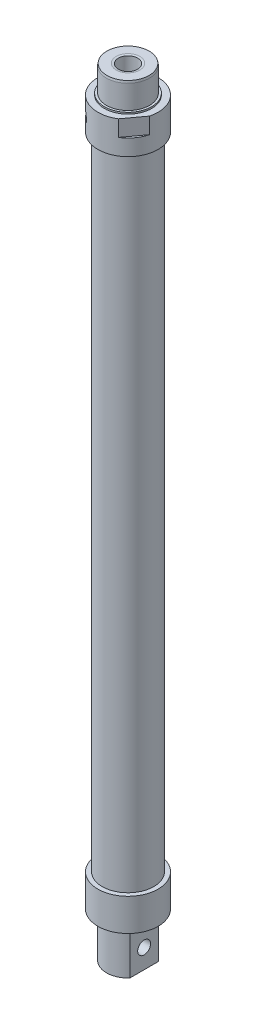
SolidWorks part; units mm, degrees
ref_plane "Front Plane" through (0, 0, 0) normal (0, 0, 1) x (1, 0, 0)
ref_plane "Top Plane" through (0, 0, 0) normal (0, 1, 0) x (1, 0, 0)
ref_plane "Right Plane" through (0, 0, 0) normal (1, 0, 0) x (0, 0, -1)
sketch "Sketch1" plane through (0, 0, 0) normal (0, 1, 0) x (1, 0, 0)
  circle A0 centre (0, 0) radius 12
  circle A1 centre (0, 0) radius 10
  dimension "D1" = 2
  dimension "D2" = 20
extrude "Boss-Extrude1" add sketch "Sketch1" along normal blind 298
sketch "Sketch2" plane through (0, 298, 0) normal (0, 1, 0) x (1, 0, 0)
  circle A0 centre (0, 0) radius 10
  circle A1 centre (0, 0) radius 14
  dimension "D1" = 20
  dimension "D2" = 4
extrude "Boss-Extrude2" add sketch "Sketch2" along normal blind 15
sketch "Sketch3" plane through (0, 313, 0) normal (0, 1, 0) x (1, 0, 0)
  line L0 (0, 0) -> (11.2894, -8.2795) construction
  line L1 (0, 0) -> (-9.5475, -10.2394) construction
  circle A0 centre (0, 0) radius 14 construction
ref_plane "Plane1" through (11.2894, 313, 8.2795) normal (0.8064, 0, 0.5914) x (0.5914, 0, -0.8064)
sketch "Sketch4" plane through (11.2894, 313, 8.2795) normal (0.8064, 0, 0.5914) x (0.5914, 0, -0.8064)
  line L0 (-6, 0) -> (6, 0)
  line L1 (-6, 0) -> (-6, -7.5)
  line L2 (6, 0) -> (6, -7.5)
  line L3 (-6, -7.5) -> (6, -7.5)
  dimension "D1" = 7.5
  dimension "D2" = 12
extrude "Cut-Extrude1" cut sketch "Sketch4" against normal blind 1 contours L0 L2 L3 L1
ref_plane "Plane2" through (0, 313, 0) normal (0.8064, 0, 0.5914) x (0.5914, 0, -0.8064)
mirror "Mirror1" about plane through (0, 313, 0) normal (0.8064, 0, 0.5914) of "Cut-Extrude1"
ref_plane "Plane3" through (-9.5475, 313, 10.2394) normal (-0.682, 0, 0.7314) x (0.7314, 0, 0.682)
sketch "Sketch5" plane through (-9.5475, 313, 10.2394) normal (-0.682, 0, 0.7314) x (0.7314, 0, 0.682)
  line L0 (0, 0) -> (13.9032, 0) construction
  circle A0 centre (0, -8) radius 2.5
  dimension "D2" = 5
  dimension "D1" = 8
extrude "Cut-Extrude2" cut sketch "Sketch5" against normal blind 5
sketch "Sketch6" plane through (0, 313, 0) normal (0, 1, 0) x (1, 0, 0)
  circle A0 centre (0, 0) radius 11
  dimension "D1" = 22
extrude "Boss-Extrude3" add sketch "Sketch6" along normal blind 0.75
sketch "Sketch7" plane through (0, 313.75, 0) normal (0, 1, 0) x (1, 0, 0)
  circle A0 centre (0, 0) radius 10
extrude "Boss-Extrude4" add sketch "Sketch7" along normal blind 12
sketch "Sketch9" plane through (0, 0, 0) normal (0, -1, 0) x (1, 0, 0)
  circle A0 centre (0, 0) radius 10
  circle A1 centre (0, 0) radius 14
  dimension "D1" = 20
  dimension "D2" = 4
extrude "Boss-Extrude6" add sketch "Sketch9" along normal blind 15
sketch "Sketch10" plane through (0, -15, 0) normal (0, -1, 0) x (1, 0, 0)
  circle A0 centre (0, 0) radius 11
  dimension "D1" = 22
extrude "Boss-Extrude7" add sketch "Sketch10" along normal blind 0.75
sketch "Sketch11" plane through (0, -15.75, 0) normal (0, -1, 0) x (1, 0, 0)
  circle A0 centre (0, 0) radius 10
  dimension "D1" = 20
extrude "Boss-Extrude8" add sketch "Sketch11" along normal blind 20
sketch "Sketch12" plane through (0, -35.75, 0) normal (0, -1, 0) x (1, 0, 0)
  line L0 (0, 0) -> (10, 0) construction
  line L1 (7.5, 6.6144) -> (7.5, -6.6144)
  line L2 (0, 10) -> (0, -10) construction
  line L3 (-7.5, 6.6144) -> (-7.5, -6.6144)
  circle A0 centre (0, 0) radius 10 construction
  circle A1 centre (0, 0) radius 10 construction
  arc A2 (7.5, 6.6144) -> (7.5, -6.6144) centre (0, 0) cw
  arc A3 (-7.5, 6.6144) -> (-7.5, -6.6144) centre (0, 0) ccw
  circle M1 centre (0, 0) radius 10
  dimension "D1" = 7.5
extrude "Cut-Extrude4" cut sketch "Sketch12" against normal blind 20 contours L3 M1 | L1 M1
sketch "Sketch13" plane through (7.5, 0, 0) normal (1, 0, 0) x (0, 0, -1)
  line L0 (0, -35.75) -> (0, -26.75) construction
  line L1 (-6.6144, -35.75) -> (6.6144, -35.75) construction
  circle A0 centre (0, -26.75) radius 3
  dimension "D1" = 9
extrude "Cut-Extrude5" cut sketch "Sketch13" against normal through all contours A0
sketch "Sketch14" plane through (0, 325.75, 0) normal (0, 1, 0) x (1, 0, 0)
  circle A0 centre (0, 0) radius 4.5
extrude "Cut-Extrude6" cut sketch "Sketch14" against normal blind 70
chamfer "Chamfer1" distance 1 angle 10 2 edges at (0, 325.75, 10) (0, 325.75, 4.5)
